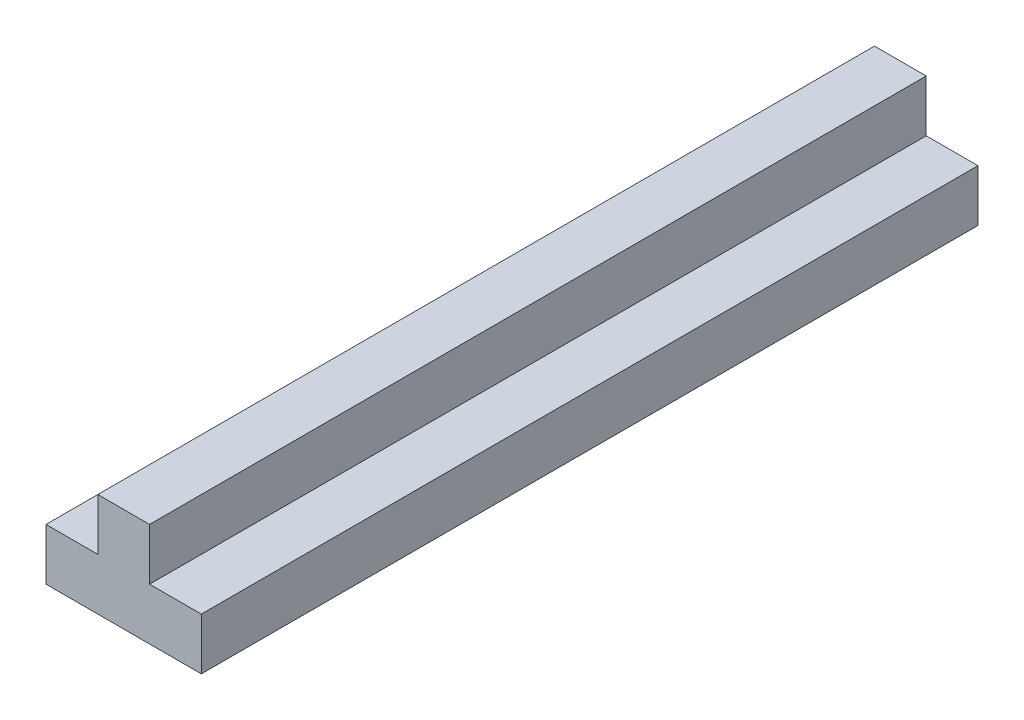
SolidWorks part; units mm, degrees
ref_plane "Front Plane" through (0, 0, 0) normal (0, 0, 1) x (1, 0, 0)
ref_plane "Top Plane" through (0, 0, 0) normal (0, 1, 0) x (1, 0, 0)
ref_plane "Right Plane" through (0, 0, 0) normal (1, 0, 0) x (0, 0, -1)
sketch "Sketch1" plane through (0, 0, 0) normal (0, 0, 1) x (1, 0, 0)
  line L1 (-6.35, -1.27) -> (6.35, -1.27)
  line L2 (-6.35, -1.27) -> (-6.35, 1.27)
  line L3 (-6.35, 1.27) -> (6.35, 1.27)
  line L4 (6.35, -1.27) -> (6.35, 1.27)
  line L5 (-6.35, -1.27) -> (6.35, 1.27) construction
  line L6 (-6.35, 1.27) -> (6.35, -1.27) construction
  point P0 (0, 0)
  dimension "D1" = 12.7
  dimension "D2" = 2.54
extrude "Boss-Extrude1" add sketch "Sketch1" along normal blind 38.1
sketch "Sketch3" plane through (6.35, 0, 0) normal (1, 0, 0) x (0, 0, -1)
  line L1 (-38.1, 1.27) -> (0, 1.27)
  line L2 (-38.1, 1.27) -> (-38.1, -1.27)
  line L3 (-38.1, -1.27) -> (0, -1.27)
  line L4 (0, 1.27) -> (0, -1.27)
extrude "Cut-Extrude1" cut sketch "Sketch3" against normal blind 2.54
sketch "Sketch4" plane through (-6.35, 0, 0) normal (-1, 0, 0) x (0, 0, 1)
  line L1 (0, 1.27) -> (38.1, 1.27)
  line L2 (0, 1.27) -> (0, -1.27)
  line L3 (0, -1.27) -> (38.1, -1.27)
  line L4 (38.1, 1.27) -> (38.1, -1.27)
extrude "Cut-Extrude2" cut sketch "Sketch4" against normal blind 2.54
sketch "Sketch5" plane through (0, 1.27, 0) normal (0, 1, 0) x (1, 0, 0)
  line L0 (3.81, 0) -> (-3.81, 0) construction
  line L1 (-1.27, 0) -> (1.27, 0)
  line L2 (-1.27, 0) -> (-1.27, -38.1)
  line L3 (-1.27, -38.1) -> (1.27, -38.1)
  line L4 (1.27, 0) -> (1.27, -38.1)
  line L5 (3.81, -38.1) -> (-3.81, -38.1) construction
  line L6 (3.81, 0) -> (3.81, -38.1) construction
  dimension "D1" = 2.54
  dimension "D2" = 2.54
extrude "Boss-Extrude3" add sketch "Sketch5" along normal blind 2.54
